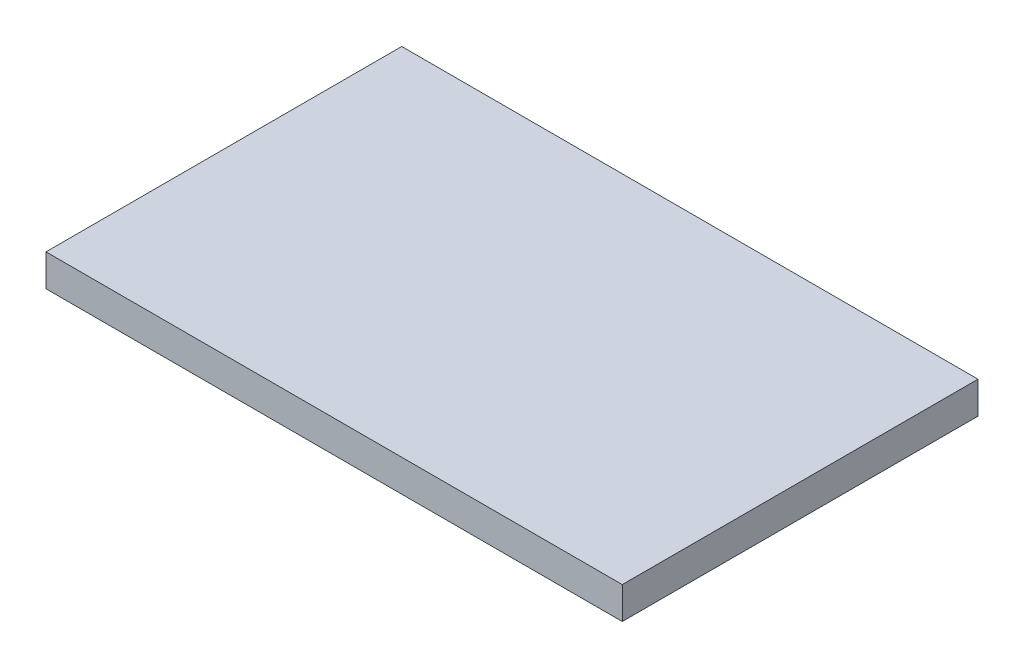
SolidWorks part; units mm, degrees
ref_plane "前基準面" through (0, 0, 0) normal (0, 0, 1) x (1, 0, 0)
ref_plane "上基準面" through (0, 0, 0) normal (0, 1, 0) x (1, 0, 0)
ref_plane "右基準面" through (0, 0, 0) normal (1, 0, 0) x (0, 0, -1)
sketch "草圖1" plane through (0, 0, 0) normal (0, 1, 0) x (1, 0, 0)
  line L1 (-40.5, 25) -> (40.5, 25)
  line L2 (-40.5, 25) -> (-40.5, -25)
  line L3 (-40.5, -25) -> (40.5, -25)
  line L4 (40.5, 25) -> (40.5, -25)
  line L5 (-40.5, 25) -> (40.5, -25) construction
  line L6 (-40.5, -25) -> (40.5, 25) construction
  point P0 (0, 0)
  dimension "D1" = 81
  dimension "D2" = 50
extrude "填料-伸長1" add sketch "草圖1" along normal blind 4.5
